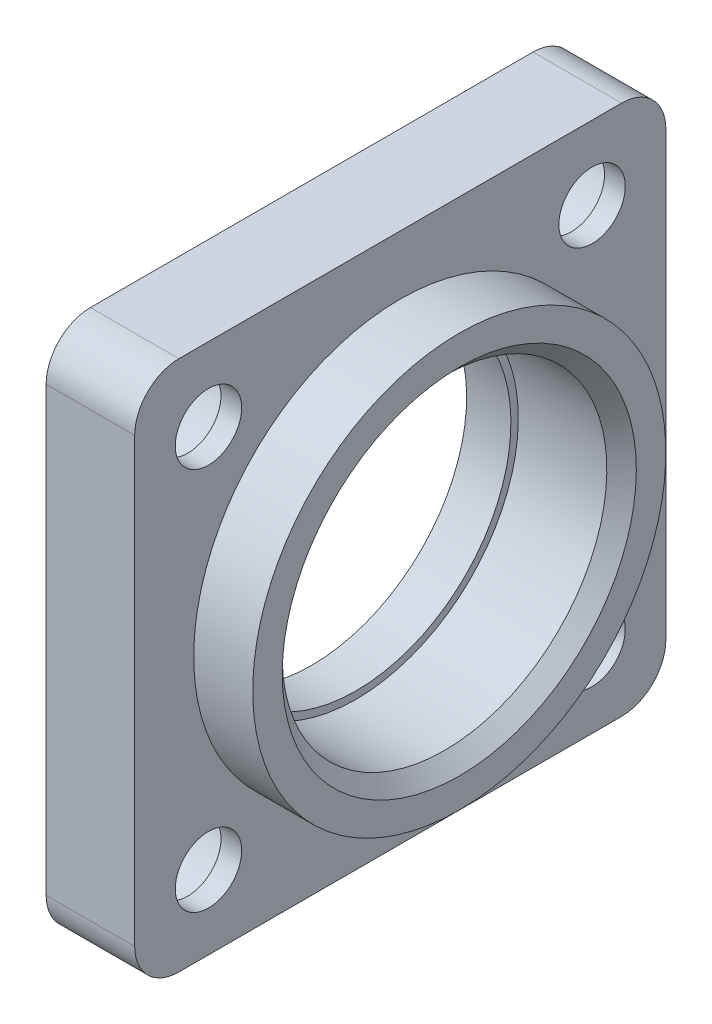
SolidWorks part; units mm, degrees
material "6061 合金"
ref_plane "前视基准面" through (0, 0, 0) normal (0, 0, 1) x (1, 0, 0)
ref_plane "上视基准面" through (0, 0, 0) normal (0, 1, 0) x (1, 0, 0)
ref_plane "右视基准面" through (0, 0, 0) normal (1, 0, 0) x (0, 0, -1)
sketch "草图1" plane through (0, 0, 0) normal (0, 0, 1) x (1, 0, 0)
  line L0 (-10.5412, 0) -> (18.5412, 0) construction
  line L1 (-6, 10.5) -> (-6, 18)
  line L2 (-6, 18) -> (0, 18)
  line L3 (0, 18) -> (0, 14)
  line L4 (0, 14) -> (4, 14)
  line L5 (4, 14) -> (4, 11)
  line L6 (-3, 11) -> (-3, 10.5)
  line L7 (-3, 11) -> (4, 11)
  line L8 (-3, 10.5) -> (-6, 10.5)
  dimension "D1" = 28
  dimension "D2" = 36
  dimension "D3" = 4
  dimension "D4" = 10
  dimension "D5" = 22
  dimension "D6" = 7
  dimension "D7" = 21
revolve "旋转1" add sketch "草图1" angle 360 about L0
hole_wizard "打孔尺寸(%根据)内六角圆柱头螺钉的类型1" [suppressed] positions "草图3" profile "草图2" counterbore size "M4" standard "GB"
sketch "草图3" plane through (-6, 0, 0) normal (-1, 0, 0) x (0, 0, 1)
  point P0 (0, 13.9464)
sketch "草图2" plane through (-6, 13.9464, 0) normal (0, 1, 0) x (0, 0, 1)
  line L0 (0, 0) -> (0, 10)
  line L1 (0, 10) -> (2.25, 10)
  line L3 (2.25, 10) -> (2.25, 4.6)
  line L4 (2.25, 4.6) -> (4, 4.6)
  line L5 (4, 4.6) -> (4, 0)
  line L7 (4, 0) -> (0, 0)
  line L11 (0, -6.35) -> (0, 107.95) construction
  dimension "通孔孔直径" = 4.5
  dimension "通孔孔深度" = 10
  dimension "柱形沉头孔直径" = 8
  dimension "柱形沉头孔深度" = 4.6
sketch "草图5" plane through (-6, 0, 0) normal (-1, 0, 0) x (0, 0, 1)
  line L1 (-18, -18) -> (18, -18)
  line L2 (-18, -18) -> (-18, 18)
  line L3 (-18, 18) -> (18, 18)
  line L4 (18, -18) -> (18, 18)
  line L5 (-18, -18) -> (18, 18) construction
  line L6 (-18, 18) -> (18, -18) construction
  circle A0 centre (0, 0) radius 18
  point P0 (0, 0)
  circle M4 centre (0, 0) radius 18
  dimension "D1" = 36
extrude "凸台-拉伸1" add sketch "草图5" against normal blind 6 contours L4 L3 M4 | L3 L2 M4 | L2 L1 M4 | L1 L4 M4
fillet "圆角1" radius 3 4 edges at (-3, -18, 18) (-3, -18, -18) (-3, 18, -18) (-3, 18, 18)
sketch "草图6" plane through (-6, 0, 0) normal (-1, 0, 0) x (0, 0, 1)
  line L1 (-13, -13) -> (13, -13)
  line L2 (-13, -13) -> (-13, 13)
  line L3 (-13, 13) -> (13, 13)
  line L4 (13, -13) -> (13, 13)
  line L5 (-13, -13) -> (13, 13) construction
  line L6 (-13, 13) -> (13, -13) construction
  point P0 (0, 0)
  dimension "D1" = 26
  dimension "D2" = 26
hole_wizard "打孔尺寸(%根据)内六角圆柱头螺钉的类型2" positions "草图8" profile "草图7" counterbore size "M4" standard "GB" end condition through all
sketch "草图8" plane through (-6, 0, 0) normal (-1, 0, 0) x (0, 0, 1)
  point P0 (-13, 13)
  point P3 (13, 13)
  point P6 (13, -13)
  point P9 (-13, -13)
sketch "草图7" plane through (-6, 13, -13) normal (0, 1, 0) x (0, 0, 1)
  line L0 (0, 0) -> (0, 10)
  line L1 (0, 10) -> (2.25, 10)
  line L3 (2.25, 10) -> (2.25, 4.6)
  line L4 (2.25, 4.6) -> (4, 4.6)
  line L5 (4, 4.6) -> (4, 0)
  line L7 (4, 0) -> (0, 0)
  line L11 (0, -6.35) -> (0, 107.95) construction
  dimension "通孔孔直径" = 4.5
  dimension "通孔孔深度" = 10
  dimension "柱形沉头孔直径" = 8
  dimension "柱形沉头孔深度" = 4.6
chamfer "倒角1" distance 1 angle 45 1 edges at (4, -11, 0)
